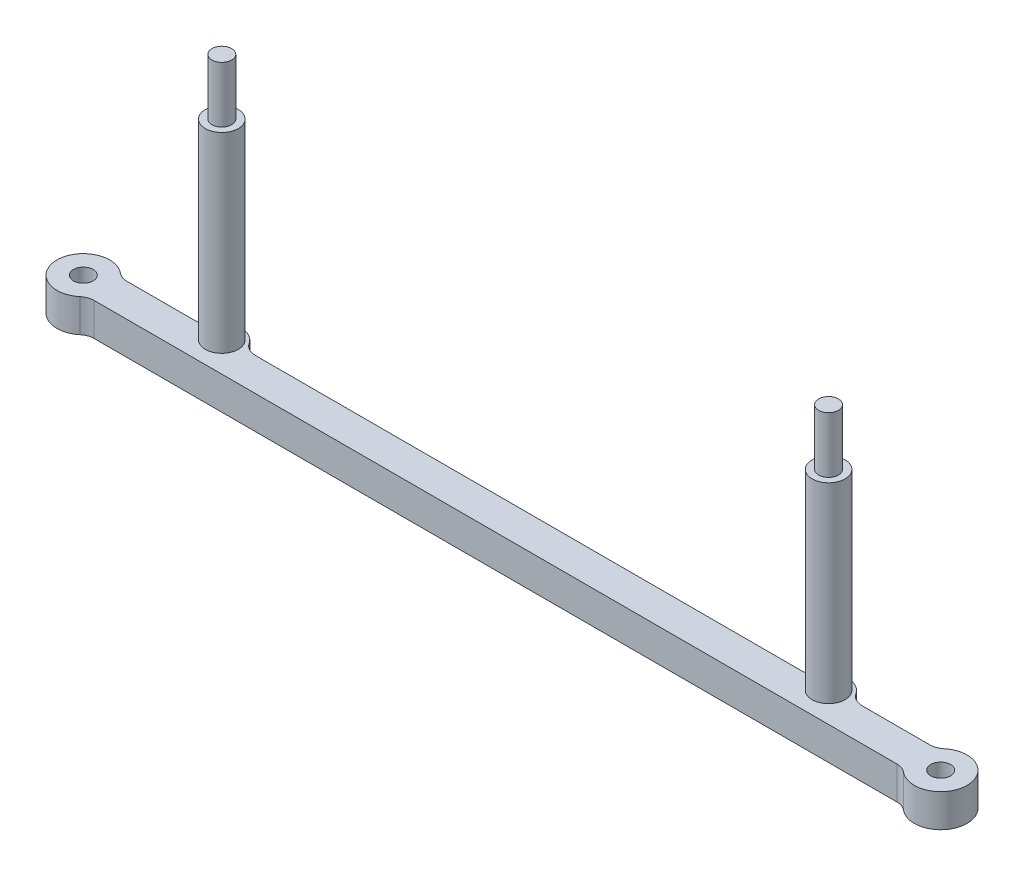
SolidWorks part; units mm, degrees
material "Delrin 2700 NC010, Low Viscosity Acetal Copolymer (SS)"
ref_plane "Front Plane" through (0, 0, 0) normal (0, 0, 1) x (1, 0, 0)
ref_plane "Top Plane" through (0, 0, 0) normal (0, 1, 0) x (1, 0, 0)
ref_plane "Right Plane" through (0, 0, 0) normal (1, 0, 0) x (0, 0, -1)
sketch "Sketch1" plane through (0, 0, 0) normal (0, 1, 0) x (1, 0, 0)
  line L0 (-65, 0) -> (65, 0) construction
  line L1 (-61.8775, 2.5) -> (61.8775, 2.5)
  line L2 (61.8775, -2.5) -> (-61.8775, -2.5)
  circle A0 centre (46, 2) radius 3
  circle A1 centre (-46, 2) radius 3
  circle A2 centre (-65, 0) radius 4
  circle A3 centre (65, 0) radius 4
  circle A4 centre (65, 0) radius 1.5
  circle A5 centre (-65, 0) radius 1.5
  dimension "D5" = 2
  dimension "D6" = 6
  dimension "D7" = 8
  dimension "D8" = 3
  dimension "D1" = 130
  dimension "D2" = 19
  dimension "D3" = 19
  dimension "D4" = 2
  dimension "D9" = 2.5
  dimension "D10" = 2.5
extrude "Boss-Extrude1" add sketch "Sketch1" along normal blind 5
fillet "Fillet1" radius 2.5 8 edges at (-48.958, 2.5, -2.5) (-43.042, 2.5, -2.5) (43.042, 2.5, -2.5) (48.958, 2.5, -2.5) (61.8775, 2.5, -2.5) (-61.8775, 2.5, 2.5) (-61.8775, 2.5, -2.5) (61.8775, 2.5, 2.5)
sketch "Sketch2" plane through (0, 5, 0) normal (0, 1, 0) x (1, 0, 0)
  circle A0 centre (-46, 2) radius 2.5
  circle A1 centre (46, 2) radius 2.5
  dimension "D1" = 5
extrude "Boss-Extrude2" add sketch "Sketch2" along normal blind 29
sketch "Sketch3" plane through (0, 34, 0) normal (0, 1, 0) x (1, 0, 0)
  circle A0 centre (-46, 2) radius 1.5
  circle A1 centre (46, 2) radius 1.5
  dimension "D1" = 3
extrude "Boss-Extrude3" add sketch "Sketch3" along normal blind 8.5
